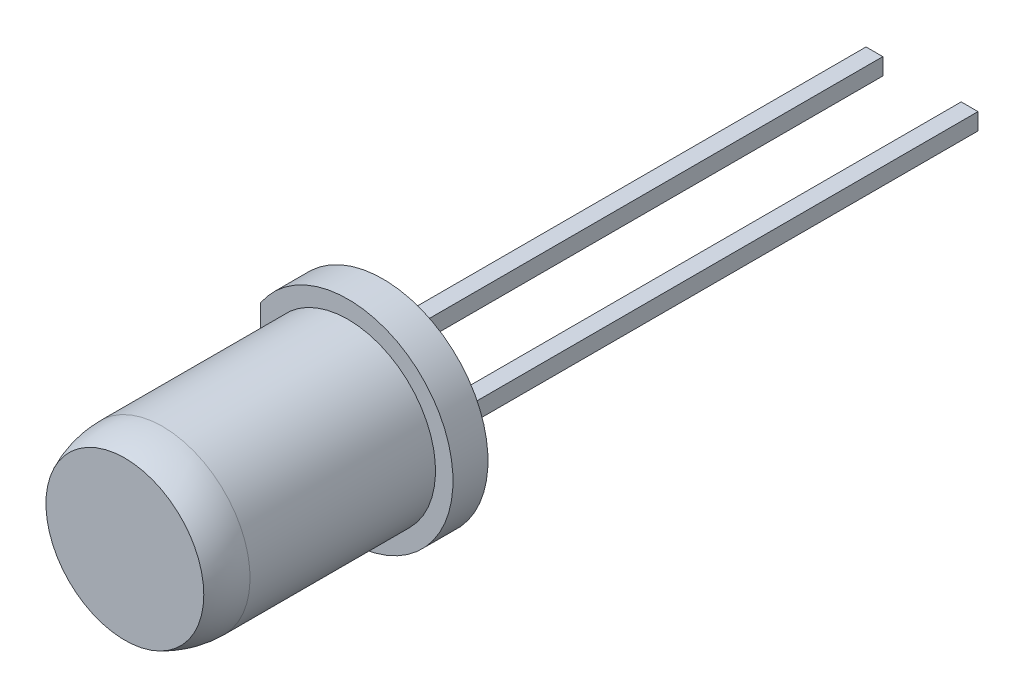
SolidWorks part; units mm, degrees
ref_plane "Plano frontal" through (0, 0, 0) normal (0, 0, 1) x (1, 0, 0)
ref_plane "Plano superior" through (0, 0, 0) normal (0, 1, 0) x (1, 0, 0)
ref_plane "Plano direito" through (0, 0, 0) normal (1, 0, 0) x (0, 0, -1)
sketch "Esboço1" plane through (0, 0, 0) normal (0, 0, 1) x (1, 0, 0)
  circle A0 centre (0, 0) radius 3
  dimension "D1" = 6
extrude "Ressalto-extrusão1" add sketch "Esboço1" along normal blind 1
sketch "Esboço3" plane through (0, 0, 0) normal (1, 0, 0) x (0, 0, -1)
  line L0 (-1, 0) -> (-8.8, 0)
  line L1 (-1, 3) -> (-1, -3) construction
  line L2 (-6.3, 2.5) -> (-1, 2.5)
  line L3 (-1, 0) -> (-1, 2.5)
  arc A0 (-8.8, 0) -> (-6.3, 2.5) centre (-6.3, 0) cw
  dimension "D1" = 2.5
  dimension "D2" = 7.8
revolve "Revolução1" add sketch "Esboço3" angle 360 about L0
sketch "Esboço4" plane through (0, 0, 0) normal (0, 0, -1) x (-1, 0, 0)
  line L0 (2.5, 1.6583) -> (2.5, -1.6583)
  circle A0 centre (0, 0) radius 3 construction
  arc A1 (2.5, -1.6583) -> (2.5, 1.6583) centre (0, 0) ccw
  circle A2 centre (0, 0) radius 2.5 construction
extrude "Corte-extrusão1" cut sketch "Esboço4" against normal up to surface (1 mm away) up to face at (2.5, 0, 1)
sketch "Esboço5" plane through (0, 0, 0) normal (0, 0, -1) x (-1, 0, 0)
  line L0 (-1.12, 0) -> (1.12, 0) construction
  line L1 (-1.6, -0.24) -> (-1.12, -0.24)
  line L2 (-1.6, -0.24) -> (-1.6, 0.24)
  line L3 (-1.6, 0.24) -> (-1.12, 0.24)
  line L4 (-1.12, -0.24) -> (-1.12, 0.24)
  line L5 (1.12, -0.24) -> (1.6, -0.24)
  line L6 (1.12, -0.24) -> (1.12, 0.24)
  line L7 (1.12, 0.24) -> (1.6, 0.24)
  line L8 (1.6, -0.24) -> (1.6, 0.24)
  dimension "D1" = 3.2
  dimension "D2" = 0.48
extrude "Ressalto-extrusão2" add sketch "Esboço5" along normal blind 25 separate body
sketch "Esboço6" plane through (0, 0, -25) normal (0, 0, -1) x (-1, 0, 0)
  line L4 (-1.6, 0.24) -> (-1.6, -0.24)
  line L5 (-1.6, -0.24) -> (-1.12, -0.24)
  line L6 (-1.12, -0.24) -> (-1.12, 0.24)
  line L7 (-1.12, 0.24) -> (-1.6, 0.24)
  line L8 (-1.6, 0.24) -> (-1.6, -0.24)
  line L9 (-1.6, -0.24) -> (-1.12, -0.24)
  line L10 (-1.12, -0.24) -> (-1.12, 0.24)
  line L11 (-1.12, 0.24) -> (-1.6, 0.24)
  dimension "D1" = 0
extrude "Ressalto-extrusão3" add sketch "Esboço6" along normal blind 2 separate body
sketch "Esboço7" plane through (0, 0, 0) normal (0, 1, 0) x (1, 0, 0)
  line L0 (-1.6, 0) -> (-1.6, -3.5)
  line L1 (-1.12, 0) -> (-1.12, -2)
  line L2 (0.02, -2) -> (1.2, -4)
  line L3 (1.2, -4) -> (-1.3, -4)
  line L4 (-1.3, -4) -> (-1.6, -3.5)
  line L5 (-1.12, -2) -> (0.02, -2)
  line L6 (1.6, 0) -> (1.6, -4)
  line L7 (1.6, -4) -> (1.4, -4)
  line L8 (1.4, -4) -> (0.22, -2)
  line L9 (0.22, -2) -> (1.12, -2)
  line L10 (1.12, -2) -> (1.12, 0)
  line L11 (-1.6, 0) -> (-1.12, 0)
  line L12 (1.12, 0) -> (1.6, 0)
  dimension "D1" = 4
  dimension "D2" = 2
  dimension "D3" = 2.8
  dimension "D4" = 0.2
  dimension "D5" = 0.9
  dimension "D6" = 3.5
  dimension "D7" = 2.5
extrude "Corte-extrusão2" cut sketch "Esboço7" against normal mid plane 0.48
sketch "Esboço8" plane through (0, 0, 0) normal (0, 1, 0) x (1, 0, 0)
  line L0 (-1.3, -4) -> (1.2, -4) construction
  line L1 (-1.6, -3.5) -> (-1.3, -4) construction
  line L2 (-1.6, 0) -> (-1.6, -3.5) construction
  line L3 (1.2, -4) -> (0.02, -2) construction
  line L4 (0.02, -2) -> (-1.12, -2) construction
  line L5 (-1.12, -2) -> (-1.12, 0) construction
  line L6 (0.22, -2) -> (1.4, -4) construction
  line L7 (1.12, -2) -> (0.22, -2) construction
  line L8 (1.12, 0) -> (1.12, -2) construction
  line L9 (1.6, -4) -> (1.6, 0) construction
  line L10 (1.4, -4) -> (1.6, -4) construction
  line L11 (-1.12, 0) -> (-1.6, 0) construction
  line L12 (1.6, 0) -> (1.12, 0) construction
  line L13 (-1.3, -4) -> (1.2, -4)
  line L14 (-1.6, -3.5) -> (-1.3, -4)
  line L15 (-1.6, 0) -> (-1.6, -3.5)
  line L16 (1.2, -4) -> (0.02, -2)
  line L17 (0.02, -2) -> (-1.12, -2)
  line L18 (-1.12, -2) -> (-1.12, 0)
  line L19 (0.22, -2) -> (1.4, -4)
  line L20 (1.12, -2) -> (0.22, -2)
  line L21 (1.12, 0) -> (1.12, -2)
  line L22 (1.6, -4) -> (1.6, 0)
  line L23 (1.4, -4) -> (1.6, -4)
  line L24 (-1.12, 0) -> (-1.6, 0)
  line L25 (1.6, 0) -> (1.12, 0)
extrude "Ressalto-extrusão4" add sketch "Esboço8" along normal mid plane 0.48 separate body
combine bodies "Combinar1" operation type add bodies to combine 109 106 104
combine bodies "Combinar2" operation type add bodies to combine 108 105
sketch "Esboço10" plane through (0, 0, 0) normal (0, 1, 0) x (1, 0, 0)
  line L0 (-0.05, -4) -> (-0.05, -3.7)
  line L1 (-1.3, -4) -> (1.2, -4) construction
  line L2 (-0.55, -4) -> (-0.05, -4)
  arc A0 (-0.05, -3.7) -> (-0.55, -4) centre (-0.05, -4.2667) ccw
  dimension "D1" = 0.5
  dimension "D2" = 0.3
revolve "Corte-Revolução1" cut sketch "Esboço10" angle 360 about L0
sketch "Esboço11" plane through (0, 0, 0) normal (0, 1, 0) x (1, 0, 0)
  line L0 (-0.55, -4) -> (-0.05, -4) construction
  line L1 (-0.05, -4) -> (-0.05, -3.7) construction
  line L2 (-0.55, -4) -> (-0.05, -4)
  line L3 (-0.05, -4) -> (-0.05, -3.7)
  arc A0 (-0.05, -3.7) -> (-0.55, -4) centre (-0.05, -4.2667) ccw construction
  arc A1 (-0.05, -3.7) -> (-0.55, -4) centre (-0.05, -4.2667) ccw
revolve "Revolução2" add sketch "Esboço11" angle 360 about L3
combine bodies "Combinar3" operation type add bodies to combine 113 112
sketch "Esboço12" plane through (0, 0, 4) normal (0, 0, 1) x (1, 0, 0)
  circle A0 centre (-0.05, 0) radius 0.2
  arc A1 (0.3886, 0.24) -> (-0.4886, 0.24) centre (-0.05, 0) ccw construction
  dimension "D1" = 0.4
extrude "Corte-extrusão3" cut sketch "Esboço12" against normal blind 0.1
sketch "Esboço13" plane through (0, 0, 0) normal (0, 1, 0) x (1, 0, 0)
  line L0 (1.6, 27) -> (-7.0603, 32)
  line L1 (1.6, 27) -> (1.12, 27) construction
  dimension "D1" = 10
  dimension "D2" = 30
ref_plane "Plano1" through (12.0913, 0, -20.9428) normal (0.5, 0, -0.866) x (-0.866, 0, -0.5)
sketch "Sketch1" plane through (0, 0, 0) normal (0, 1, 0) x (1, 0, 0)
  line L1 (-10.9818, -7.3779) -> (9.9237, -7.3779)
  line L2 (-10.9818, -7.3779) -> (-10.9818, 15.4043)
  line L3 (-10.9818, 15.4043) -> (9.9237, 15.4043)
  line L4 (9.9237, -7.3779) -> (9.9237, 15.4043)
  line L5 (-19.4137, -30.0635) -> (21.0898, -30.0635)
  line L6 (-19.4137, -30.0635) -> (-19.4137, 33.3093)
  line L7 (-19.4137, 33.3093) -> (21.0898, 33.3093)
  line L8 (21.0898, -30.0635) -> (21.0898, 33.3093)
extrude "Cut-Extrude1" cut sketch "Sketch1" against normal through all both and the other way through all
